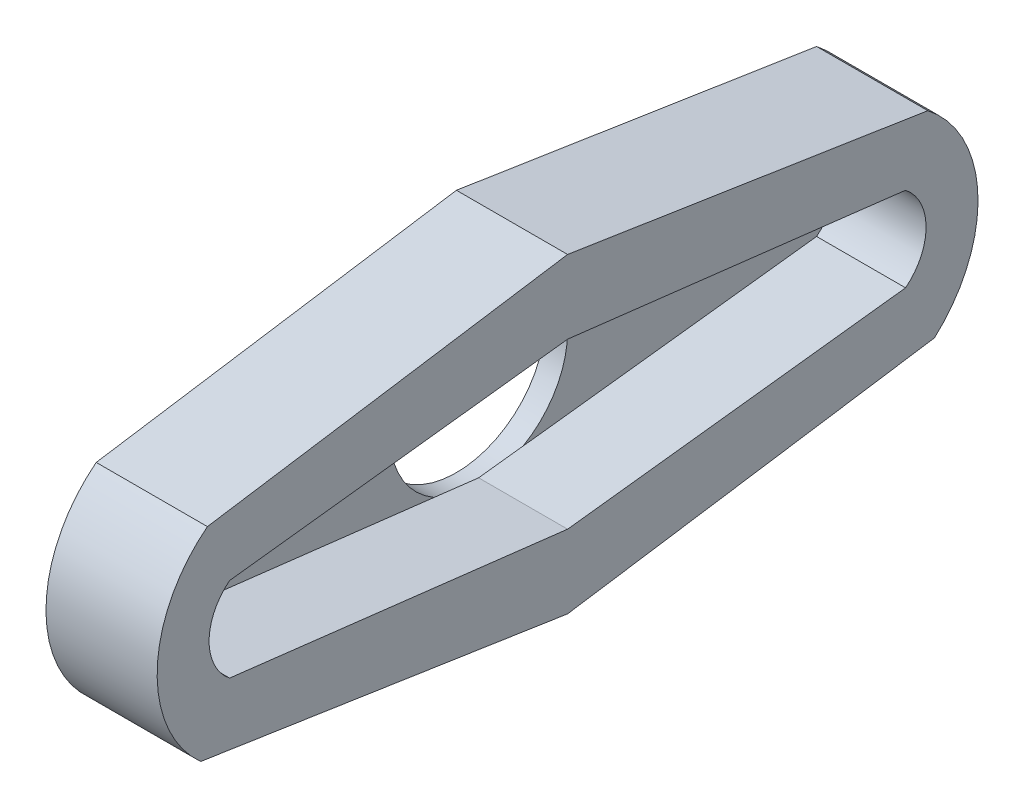
SolidWorks part; units mm, degrees
ref_plane "Front Plane" through (0, 0, 0) normal (0, 0, 1) x (1, 0, 0)
ref_plane "Top Plane" through (0, 0, 0) normal (0, 1, 0) x (1, 0, 0)
ref_plane "Right Plane" through (0, 0, 0) normal (1, 0, 0) x (0, 0, -1)
sketch "Sketch1" plane through (0, 0, 0) normal (1, 0, 0) x (0, 0, -1)
  line L0 (0, 7) -> (-16.2, 4.5)
  line L1 (-16.5, -4.5) -> (0, -7)
  line L4 (0, 3.7) -> (-15.2, 1.9)
  line L5 (-15.2, -1.9) -> (0, -3.7)
  line L10 (0, 0) -> (0, 22.8337) construction
  line L11 (15.2, -1.9) -> (0, -3.7)
  line L12 (0, 3.7) -> (15.2, 1.9)
  line L13 (16.5, -4.5) -> (0, -7)
  line L14 (0, 7) -> (16.2, 4.5)
  arc A0 (-16.2, 4.5) -> (-16.5, -4.5) centre (-12.5962, -0.1251) ccw
  arc A1 (-15.2, 1.9) -> (-15.2, -1.9) centre (-13.7067, 0) ccw
  arc A2 (15.2, 1.9) -> (15.2, -1.9) centre (13.7067, 0) cw
  arc A3 (16.2, 4.5) -> (16.5, -4.5) centre (12.5962, -0.1251) cw
  dimension "D1" = 2.5
  dimension "D2" = 2.5
  dimension "D3" = 1.8
  dimension "D4" = 1.8
  dimension "D5" = 15.2
  dimension "D6" = 0
  dimension "D7" = 16.2
  dimension "D8" = 0
  dimension "D9" = 0
  dimension "D11" = 15.2
  dimension "D12" = 16.5
  dimension "D13" = 0
extrude "Boss-Extrude1" add sketch "Sketch1" along normal blind 4
sketch "Sketch2" plane through (0, 0, 0) normal (1, 0, 0) x (0, 0, -1)
  line L0 (0, 7) -> (-16.2, 4.5)
  line L1 (-16.5, -4.5) -> (0, -7)
  line L2 (0, -8.5344) -> (0, 10.0066) construction
  line L3 (16.5, -4.5) -> (0, -7)
  line L4 (0, 7) -> (16.2, 4.5)
  arc A0 (-16.2, 4.5) -> (-16.5, -4.5) centre (-12.5962, -0.1251) ccw
  arc A1 (16.2, 4.5) -> (16.5, -4.5) centre (12.5962, -0.1251) cw
  circle A2 centre (0, 0) radius 4
  dimension "D1" = 8
extrude "Boss-Extrude2" add sketch "Sketch2" against normal blind 1
